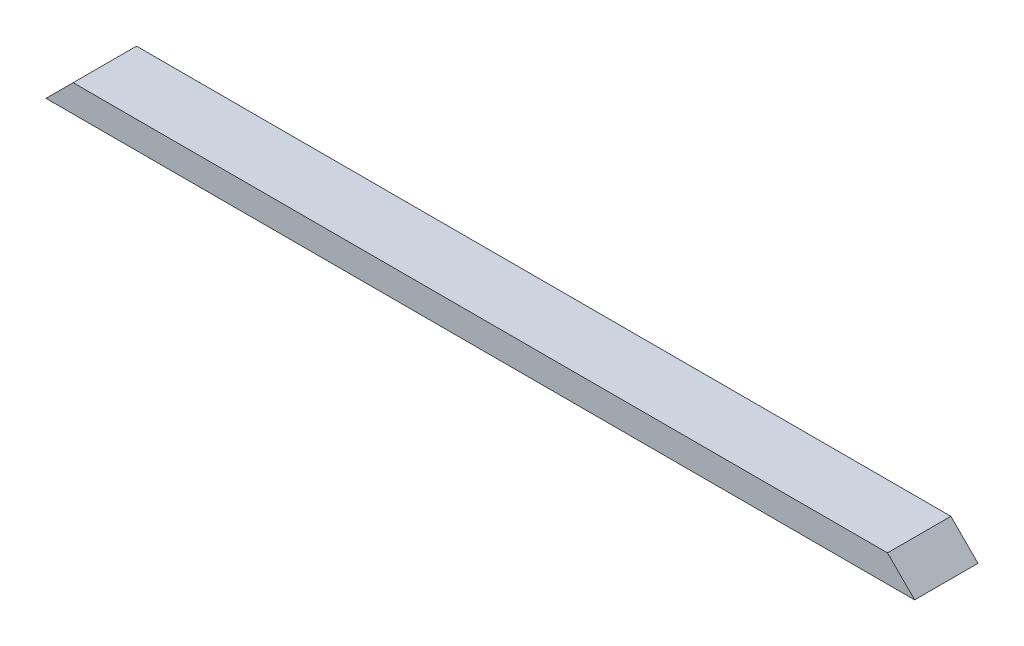
SolidWorks part; units mm, degrees
material "Pine"
ref_plane "Front Plane" through (0, 0, 0) normal (0, 0, 1) x (1, 0, 0)
ref_plane "Top Plane" through (0, 0, 0) normal (0, 1, 0) x (1, 0, 0)
ref_plane "Right Plane" through (0, 0, 0) normal (1, 0, 0) x (0, 0, -1)
sketch "Sketch1" plane through (0, 0, 0) normal (0, 1, 0) x (1, 0, 0)
  line L1 (0, 0) -> (1219.2, 0)
  line L2 (0, 0) -> (0, 88.9)
  line L3 (0, 88.9) -> (1219.2, 88.9)
  line L4 (1219.2, 0) -> (1219.2, 88.9)
  dimension "D1" = 88.9
  dimension "D2" = 1219.2
extrude "Boss-Extrude1" add sketch "Sketch1" along normal blind 38.1
sketch "Sketch2" plane through (0, 0, 0) normal (0, 0, 1) x (1, 0, 0)
  line L0 (0, 0) -> (38.1, 38.1)
  line L1 (0, 38.1) -> (1219.2, 38.1) construction
  line L2 (38.1, 38.1) -> (0, 38.1)
  line L3 (0, 38.1) -> (0, 0)
  line L5 (1219.2, 0) -> (1219.2, 38.1)
  line L9 (1219.2, 38.1) -> (1181.1, 38.1)
  line L10 (1181.1, 38.1) -> (1219.2, 0)
  dimension "D1" = 38.1
  dimension "D2" = 38.1
  dimension "D3" = 38.1
extrude "Cut-Extrude1" cut sketch "Sketch2" against normal through all
